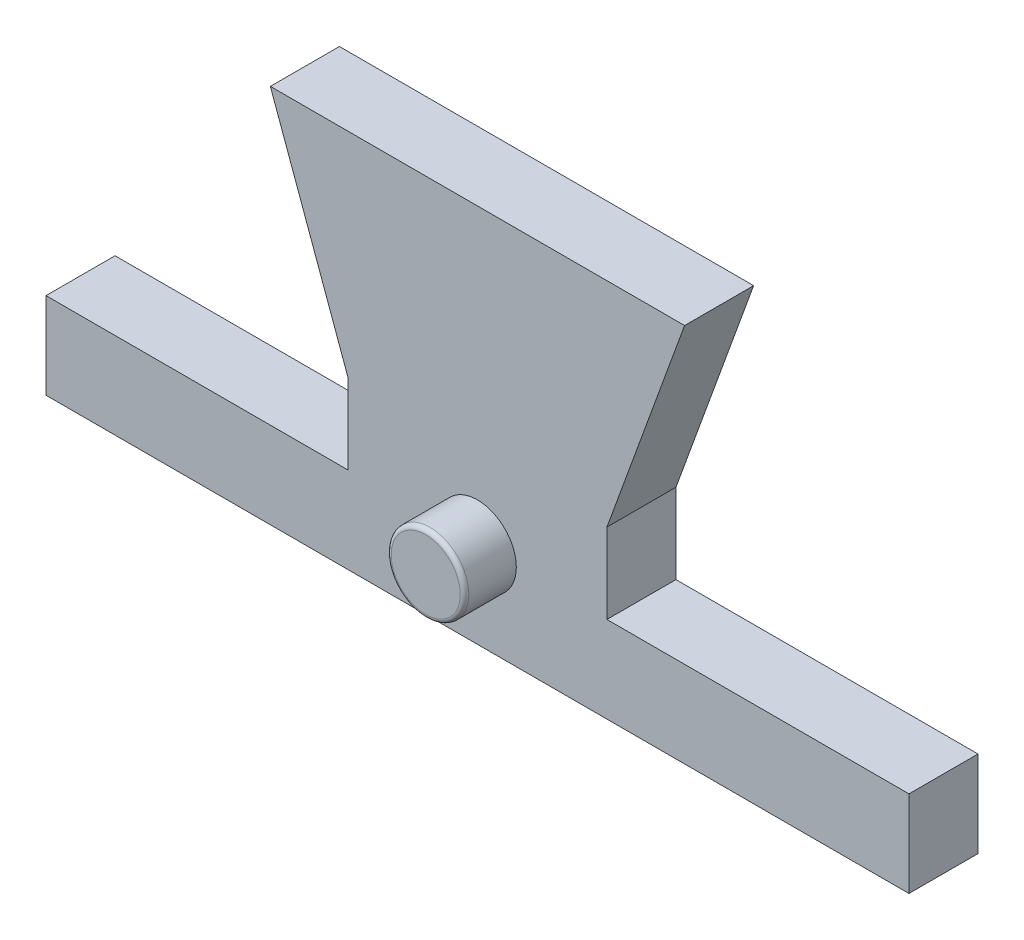
SolidWorks part; units mm, degrees
ref_plane "Front" through (0, 0, 0) normal (0, 0, 1) x (1, 0, 0)
ref_plane "Top" through (0, 0, 0) normal (0, 1, 0) x (1, 0, 0)
ref_plane "Right" through (0, 0, 0) normal (1, 0, 0) x (0, 0, -1)
sketch "Sketch1" plane through (0, 0, 0) normal (0, 0, 1) x (1, 0, 0)
  line L0 (0, 0) -> (-50, 0)
  line L1 (-50, 0) -> (-50, 5)
  line L2 (-50, 5) -> (-32.5, 5)
  line L3 (-32.5, 5) -> (-32.5, 22)
  line L4 (-32.5, 22) -> (-17.5, 22)
  line L5 (-17.5, 22) -> (-17.5, 5)
  line L6 (-17.5, 5) -> (0, 5)
  line L7 (0, 5) -> (0, 0)
  line L8 (-13, 22) -> (-17.5, 9.6364)
  line L9 (-37, 22) -> (-32.5, 9.6364)
  line L10 (-37, 22) -> (-32.5, 22)
  line L11 (-13, 22) -> (-17.5, 22)
  line L12 (-13, 22) -> (-17.5, 22)
  line L13 (-32.5, 22) -> (-37, 22)
  dimension "D1" = 50
  dimension "D2" = 5
  dimension "D5" = 15
  dimension "D6" = 22
  dimension "D3" = 20
  dimension "D4" = 20
  dimension "D7" = 24
extrude "Boss-Extrude1" add sketch "Sketch1" along normal blind 4
sketch "Sketch2" plane through (0, 0, 4) normal (0, 0, 1) x (1, 0, 0)
  line L0 (-25, 5) -> (-25, 0)
  line L8 (0, 0) -> (0, 5)
  line L9 (0, 5) -> (-17.5, 5)
  line L10 (-17.5, 5) -> (-17.5, 9.6364)
  line L11 (-13, 22) -> (-37, 22)
  line L12 (-17.5, 5) -> (-17.5, 9.6364)
  line L13 (-32.5, 5) -> (-50, 5)
  line L14 (-50, 5) -> (-50, 0)
  line L15 (-50, 0) -> (0, 0)
  line L16 (0, 0) -> (0, 5)
  line L17 (0, 5) -> (-17.5, 5)
  line L19 (-13, 22) -> (-37, 22)
  line L21 (-32.5, 5) -> (-50, 5)
  line L22 (-50, 5) -> (-50, 0)
  line L23 (-50, 0) -> (0, 0)
  line L27 (-17.5, 9.6364) -> (-13, 22)
  line L28 (-17.5, 9.6364) -> (-13, 22)
  line L29 (-37, 22) -> (-32.5, 9.6364)
  line L30 (-37, 22) -> (-32.5, 9.6364)
  line L31 (-32.5, 9.6364) -> (-32.5, 5)
  line L32 (-32.5, 9.6364) -> (-32.5, 5)
  circle A0 centre (-25, 5) radius 2.25
  dimension "D3" = 4.5
  dimension "D2" = 5
  dimension "D1" = 0
extrude "Boss-Extrude2" add sketch "Sketch2" along normal blind 3 and the other way blind 7
fillet "Fillet1" radius 0.25 2 edges at (-22.75, 5, -3) (-22.75, 5, 7)
equation "\"D4@Sketch1\"=\"D3@Sketch1\""
